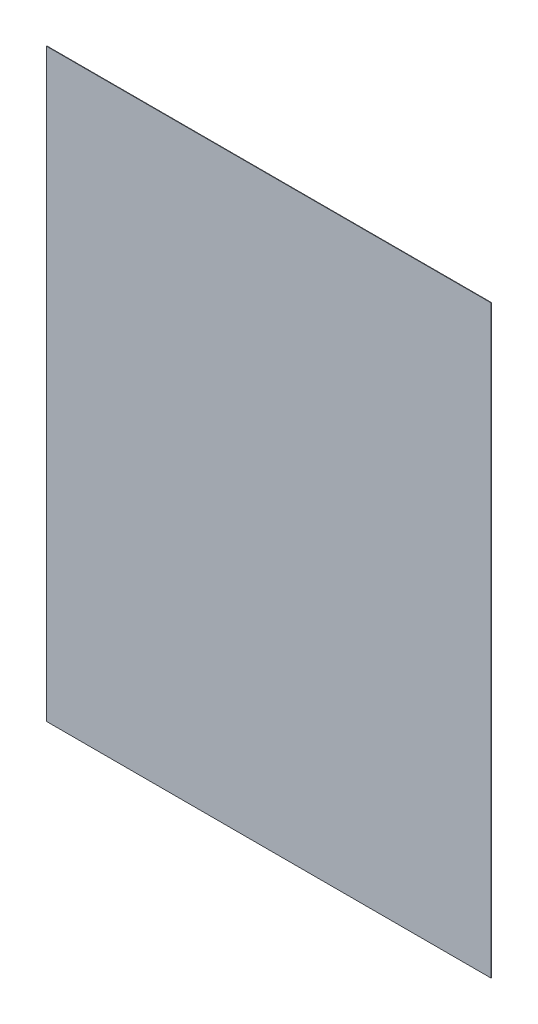
SolidWorks part; units mm, degrees
material "A123 Amp20 Positive"
ref_plane "Front Plane" through (0, 0, 0) normal (0, 0, 1) x (1, 0, 0)
ref_plane "Top Plane" through (0, 0, 0) normal (0, 1, 0) x (1, 0, 0)
ref_plane "Right Plane" through (0, 0, 0) normal (1, 0, 0) x (0, 0, -1)
sketch "Sketch1" plane through (0, 0, 0) normal (0, 0, 1) x (1, 0, 0)
  line L1 (-78.05, 102.75) -> (78.05, 102.75)
  line L2 (-78.05, 102.75) -> (-78.05, -102.75)
  line L3 (-78.05, -102.75) -> (78.05, -102.75)
  line L4 (78.05, 102.75) -> (78.05, -102.75)
  line L5 (-78.05, 102.75) -> (78.05, -102.75) construction
  line L6 (-78.05, -102.75) -> (78.05, 102.75) construction
  point P0 (0, 0)
  dimension "D1" = 156.1
  dimension "D2" = 205.5
extrude "Positive" add sketch "Sketch1" along normal blind 0.1591
